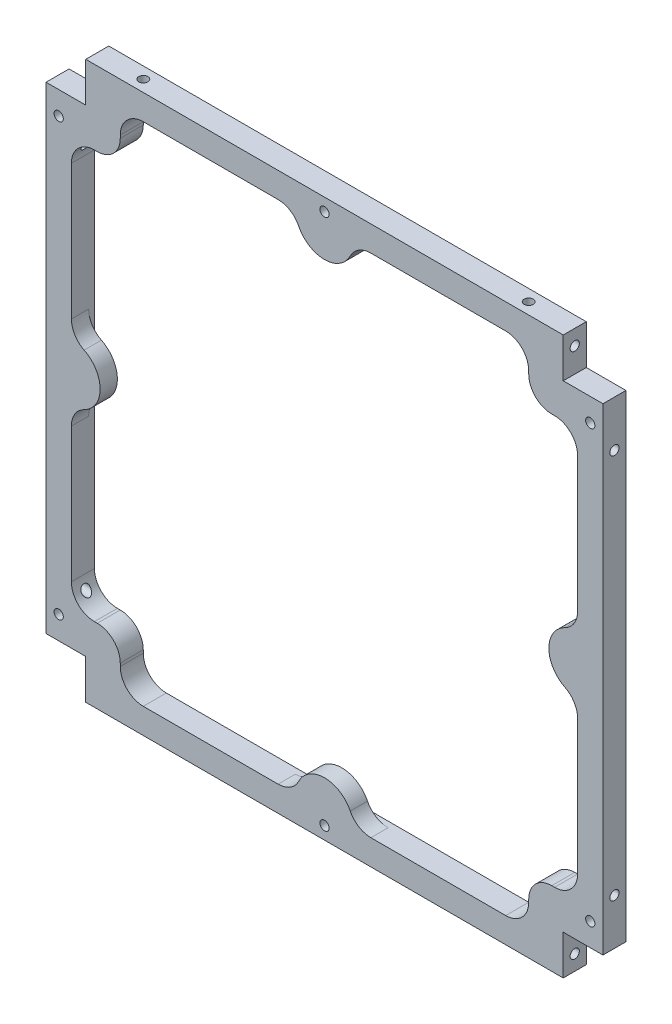
SolidWorks part; units mm, degrees
material "6061-T6 (SS)"
ref_plane "Front Plane" through (0, 0, 0) normal (0, 0, 1) x (1, 0, 0)
ref_plane "Top Plane" through (0, 0, 0) normal (0, 1, 0) x (1, 0, 0)
ref_plane "Right Plane" through (0, 0, 0) normal (1, 0, 0) x (0, 0, -1)
sketch "Sketch3" plane through (0, 0, 0) normal (0, 0, 1) x (1, 0, 0)
  line L1 (0, 0) -> (100, 0)
  line L2 (0, 0) -> (0, -100)
  line L3 (0, -100) -> (100, -100)
  line L4 (100, 0) -> (100, -100)
  dimension "D1" = 100
  dimension "D2" = 100
extrude "Boss-Extrude2" add sketch "Sketch3" along normal blind 4
sketch "Sketch4" plane through (0, 0, 0) normal (0, 0, -1) x (-1, 0, 0)
  line L1 (0, -100) -> (-8.5, -100)
  line L2 (0, -100) -> (0, -91.5)
  line L3 (0, -91.5) -> (-8.5, -91.5)
  line L4 (-8.5, -100) -> (-8.5, -91.5)
  line L5 (0, 0) -> (-8.5, 0)
  line L6 (0, 0) -> (0, -8.5)
  line L7 (0, -8.5) -> (-8.5, -8.5)
  line L8 (-8.5, 0) -> (-8.5, -8.5)
  line L9 (-100, 0) -> (-91.5, 0)
  line L10 (-100, 0) -> (-100, -8.5)
  line L11 (-100, -8.5) -> (-91.5, -8.5)
  line L12 (-91.5, 0) -> (-91.5, -8.5)
  line L14 (-100, -100) -> (-91.5, -100)
  line L15 (-100, -100) -> (-100, -91.5)
  line L16 (-100, -91.5) -> (-91.5, -91.5)
  line L17 (-91.5, -100) -> (-91.5, -91.5)
  dimension "D1" = 8.5
extrude "Cut-Extrude1" cut sketch "Sketch4" against normal through all
sketch "Sketch5" plane through (0, 0, 0) normal (0, 0, -1) x (-1, 0, 0)
  line L0 (-100, -91.5) -> (-100, -8.5) construction
  line L1 (-94, -14.5) -> (-85.5, -14.5)
  line L2 (-94, -14.5) -> (-94, -85.5)
  line L3 (-94, -85.5) -> (-85.5, -85.5)
  line L4 (-6, -14.5) -> (-6, -85.5)
  line L5 (-14.5, -14.5) -> (-14.5, -6)
  line L6 (-8.5, -100) -> (-91.5, -100) construction
  line L8 (-85.5, -6) -> (-14.5, -6)
  line L9 (-14.5, -85.5) -> (-14.5, -94)
  line L10 (-14.5, -94) -> (-85.5, -94)
  line L11 (-85.5, -94) -> (-85.5, -85.5)
  line L12 (-85.5, -14.5) -> (-85.5, -6)
  line L13 (-14.5, -14.5) -> (-6, -14.5)
  line L14 (-91.5, -8.5) -> (-91.5, 0) construction
  line L15 (-8.5, 0) -> (-8.5, -8.5) construction
  line L16 (-100, -8.5) -> (-91.5, -8.5) construction
  line L18 (-14.5, -85.5) -> (-6, -85.5)
  line L19 (-91.5, -91.5) -> (-100, -91.5) construction
  line L21 (-91.5, 0) -> (-8.5, 0) construction
  line L22 (0, -8.5) -> (0, -91.5) construction
  dimension "D1" = 6
  dimension "D2" = 6
  dimension "D3" = 6
  dimension "D4" = 6
  dimension "D5" = 6
  dimension "D6" = 6
  dimension "D7" = 6
  dimension "D8" = 6
extrude "Cut-Extrude2" cut sketch "Sketch5" against normal through all
fillet "Fillet4" radius 4 4 edges at (85.5, -85.5, 2) (14.5, -85.5, 2) (14.5, -14.5, 2) (85.5, -14.5, 2)
fillet "Fillet6" radius 4 8 edges at (85.5, -94, 2) (14.5, -94, 2) (6, -85.5, 2) (14.5, -6, 2) (6, -14.5, 2) (85.5, -6, 2) (94, -14.5, 2) (94, -85.5, 2)
sketch "Sketch6" plane through (0, 0, 4) normal (0, 0, 1) x (1, 0, 0)
  line L0 (6, -81.5) -> (6, -18.5) construction
  line L1 (94, -18.5) -> (94, -81.5) construction
  line L2 (6, -45) -> (6, -55)
  line L3 (94, -45) -> (94, -55)
  line L4 (18.5, -6) -> (81.5, -6) construction
  line L5 (81.5, -94) -> (18.5, -94) construction
  line L6 (45, -6) -> (55, -6)
  line L7 (45, -94) -> (55, -94)
  arc A0 (6, -55) -> (6, -45) centre (6, -50) ccw
  arc A1 (94, -45) -> (94, -55) centre (94, -50) ccw
  arc A2 (45, -6) -> (55, -6) centre (50, -6) ccw
  arc A3 (55, -94) -> (45, -94) centre (50, -94) ccw
  dimension "D1" = 10
  dimension "D2" = 10
  dimension "D3" = 10
  dimension "D4" = 10
extrude "Boss-Extrude3" add sketch "Sketch6" against normal offset from surface (3 mm away) 1 up to face at (50, -50, 0)
hole_wizard "M2x0.4 Tapped Hole1" positions "Sketch8" profile "Sketch7" tap size "M2x0.4" standard "ANSI Metric"
sketch "Sketch8" plane through (0, 0, 4) normal (0, 0, 1) x (1, 0, 0)
  line L1 (45, -94) -> (18.5, -94) construction
  line L2 (6, -45) -> (6, -18.5) construction
  line L3 (55, -6) -> (81.5, -6) construction
  line L4 (94, -55) -> (94, -81.5) construction
  line L5 (6, -81.5) -> (6, -55) construction
  line L6 (8.5, -8.5) -> (0, -8.5) construction
  line L7 (0, -91.5) -> (8.5, -91.5) construction
  line L8 (94, -18.5) -> (94, -45) construction
  line L9 (91.5, -91.5) -> (100, -91.5) construction
  line L10 (100, -8.5) -> (91.5, -8.5) construction
  point P12 (50, -3.8)
  point P14 (3.8, -12.5)
  point P16 (50, -96.2)
  point P18 (96.2, -87.5)
  point P29 (3.8, -87.5)
  point P38 (96.2, -12.5)
  dimension "D1" = 2.2
  dimension "D2" = 2.2
  dimension "D3" = 2.2
  dimension "D4" = 2.2
  dimension "D5" = 2.2
  dimension "D6" = 4
  dimension "D7" = 4
  dimension "D8" = 2.2
  dimension "D9" = 4
  dimension "D10" = 4
sketch "Sketch7" plane through (50, -3.8, 4) normal (1, 0, 0) x (0, -1, 0)
  line L0 (0, 0) -> (0, 5.6807)
  line L1 (0, 5.6807) -> (0.8, 5.2)
  line L2 (0.8, 5.2) -> (0.8, 0)
  line L5 (0.8, 0) -> (0, 0)
  line L10 (0, 5.6807) -> (-0.8, 5.2) construction
  line L11 (0, -6.35) -> (0, 107.95) construction
  dimension "Tap Drill Dia." = 1.6
  dimension "Tap Drill Depth" = 5.2
  dimension "Drill Angle" = 118
cosmetic thread "Hole Thread9" parameters "D1"=4, "D2"=2
cosmetic thread "Hole Thread10" parameters "D1"=4, "D2"=2
cosmetic thread "Hole Thread11" parameters "D1"=4, "D2"=2
cosmetic thread "Hole Thread12" parameters "D1"=4, "D2"=2
cosmetic thread "Cosmetic Thread1" parameters "D1"=4, "D2"=2
cosmetic thread "Cosmetic Thread2" parameters "D1"=4, "D2"=2
hole_wizard "M2x0.4 Tapped Hole2" positions "Sketch10" profile "Sketch9" tap size "M2x0.4" standard "ANSI Metric"
sketch "Sketch10" plane through (0, 0, 0) normal (0, 1, 0) x (1, 0, 0)
  line L0 (18.5, 0) -> (81.5, 0) construction
  line L1 (91.5, -4) -> (91.5, 0) construction
  line L2 (8.5, -4) -> (8.5, 0) construction
  point P10 (83.5, -2)
  point P13 (16.5, -2)
  dimension "D1" = 2
  dimension "D2" = 8
  dimension "D3" = 8
cosmetic thread "Hole Thread31" parameters "D2"=2
cosmetic thread "Hole Thread32" parameters "D2"=2
sketch "Sketch9" plane through (83.5, 0, 2) normal (1, 0, 0) x (0, 0, 1)
  line L0 (0, 0) -> (0, 6.5359)
  line L1 (0, 6.5359) -> (0.8, 6.5359)
  line L2 (0.8, 6.5359) -> (0.8, 0)
  line L5 (0.8, 0) -> (0, 0)
  line L11 (0, -6.35) -> (0, 107.95) construction
  dimension "Thru Tap Drill Dia." = 1.6
  dimension "Thru Tap Drill Depth" = 6.5359
hole_wizard "M2x0.4 Tapped Hole3" positions "Sketch12" profile "Sketch11" tap size "M2x0.4" standard "ANSI Metric"
sketch "Sketch12" plane through (100, 0, 0) normal (1, 0, 0) x (0, 0, -1)
  line L0 (0, -91.5) -> (0, -8.5) construction
  line L1 (-4, -8.5) -> (0, -8.5) construction
  line L2 (-4, -91.5) -> (0, -91.5) construction
  point P0 (-2, -83.5)
  point P3 (-2, -16.5)
  dimension "D1" = 2
  dimension "D2" = 8
  dimension "D3" = 8
cosmetic thread "Hole Thread30" parameters "D1"=4, "D2"=2
cosmetic thread "Hole Thread33" parameters "D1"=4, "D2"=2
sketch "Sketch11" plane through (100, -83.5, 2) normal (0, 1, 0) x (0, 0, -1)
  line L0 (0, 0) -> (0, 9.0007)
  line L1 (0, 9.0007) -> (0.8, 8.52)
  line L2 (0.8, 8.52) -> (0.8, 0)
  line L5 (0.8, 0) -> (0, 0)
  line L10 (0, 9.0007) -> (-0.8, 8.52) construction
  line L11 (0, -6.35) -> (0, 107.95) construction
  dimension "Tap Drill Dia." = 1.6
  dimension "Tap Drill Depth" = 8.52
  dimension "Drill Angle" = 118
hole_wizard "M2x0.4 Tapped Hole13" positions "Sketch16" profile "Sketch15" tap size "M2x0.4" standard "Ansi Metric" end condition up to next
sketch "Sketch16" plane through (0, 0, 0) normal (-1, 0, 0) x (0, 0, 1)
  line L0 (4, -8.5) -> (4, -91.5) construction
  line L1 (4, -91.5) -> (0, -91.5) construction
  line L2 (4, -8.5) -> (0, -8.5) construction
  point P3 (2, -83.5)
  point P18 (2, -16.5)
  dimension "D1" = 2
  dimension "D2" = 8
  dimension "D3" = 8
cosmetic thread "Hole Thread22" parameters "D2"=2
cosmetic thread "Hole Thread34" parameters "D2"=2
sketch "Sketch15" plane through (0, -83.5, 2) normal (0, 1, 0) x (0, 0, 1)
  line L0 (0, 0) -> (0, 6.5359)
  line L1 (0, 6.5359) -> (0.8, 6.5359)
  line L2 (0.8, 6.5359) -> (0.8, 0)
  line L5 (0.8, 0) -> (0, 0)
  line L11 (0, -6.35) -> (0, 107.95) construction
  dimension "次ｻｰﾌｪｽまでのねじ下穴ﾄﾞﾘﾙ直径" = 1.6
  dimension "次ｻｰﾌｪｽまでのねじ下穴ﾄﾞﾘﾙの深さ" = 6.5359
hole_wizard "M2x0.4 Tapped Hole5" positions "Sketch18" profile "Sketch17" tap size "M2x0.4" standard "ANSI Metric"
sketch "Sketch18" plane through (0, -100, 0) normal (0, -1, 0) x (-1, 0, 0)
  line L0 (-8.5, -4) -> (-91.5, -4) construction
  line L1 (-8.5, -4) -> (-8.5, 0) construction
  line L2 (-91.5, -4) -> (-91.5, 0) construction
  point P0 (-16.5, -2)
  point P3 (-83.5, -2)
  dimension "D1" = 2
  dimension "D2" = 8
  dimension "D3" = 8
sketch "Sketch17" plane through (16.5, -100, 2) normal (1, 0, 0) x (0, 0, -1)
  line L0 (0, 0) -> (0, 6.4807)
  line L1 (0, 6.4807) -> (0.8, 6)
  line L2 (0.8, 6) -> (0.8, 0)
  line L5 (0.8, 0) -> (0, 0)
  line L10 (0, 6.4807) -> (-0.8, 6) construction
  line L11 (0, -6.35) -> (0, 107.95) construction
  dimension "Tap Drill Dia." = 1.6
  dimension "Tap Drill Depth" = 6
  dimension "Drill Angle" = 118
cosmetic thread "Hole Thread23" parameters "D1"=4, "D2"=2
cosmetic thread "Hole Thread24" parameters "D1"=4, "D2"=2
fillet "Fillet7" radius 4 1 edges at (6, -45, 2.5)
fillet "Fillet8" radius 4 7 edges at (45, -94, 2.5) (55, -94, 2.5) (45, -6, 2.5) (55, -6, 2.5) (94, -45, 2.5) (94, -55, 2.5) (6, -55, 2.5)
hole_wizard "M2x0.4 Tapped Hole9" positions "Sketch30" profile "Sketch29" tap size "M2x0.4" standard "ANSI Metric"
sketch "Sketch30" plane through (8.5, 0, 0) normal (-1, 0, 0) x (0, 0, 1)
  point P0 (2, -95.75)
sketch "Sketch29" plane through (8.5, -95.75, 2) normal (0, 1, 0) x (0, 0, 1)
  line L0 (0, 0) -> (0, 6.4807)
  line L1 (0, 6.4807) -> (0.8, 6)
  line L2 (0.8, 6) -> (0.8, 0)
  line L5 (0.8, 0) -> (0, 0)
  line L10 (0, 6.4807) -> (-0.8, 6) construction
  line L11 (0, -6.35) -> (0, 107.95) construction
  dimension "Tap Drill Dia." = 1.6
  dimension "Tap Drill Depth" = 6
  dimension "Drill Angle" = 118
cosmetic thread "Hole Thread35" parameters "D1"=4, "D2"=2
hole_wizard "M2x0.4 Tapped Hole10" positions "Sketch32" profile "Sketch31" tap size "M2x0.4" standard "ANSI Metric"
sketch "Sketch32" plane through (8.5, 0, 0) normal (-1, 0, 0) x (0, 0, 1)
  point P0 (2, -4.25)
sketch "Sketch31" plane through (8.5, -4.25, 2) normal (0, 1, 0) x (0, 0, 1)
  line L0 (0, 0) -> (0, 6.4807)
  line L1 (0, 6.4807) -> (0.8, 6)
  line L2 (0.8, 6) -> (0.8, 0)
  line L5 (0.8, 0) -> (0, 0)
  line L10 (0, 6.4807) -> (-0.8, 6) construction
  line L11 (0, -6.35) -> (0, 107.95) construction
  dimension "Tap Drill Dia." = 1.6
  dimension "Tap Drill Depth" = 6
  dimension "Drill Angle" = 118
cosmetic thread "Hole Thread36" parameters "D1"=4, "D2"=2
sketch "Sketch33" plane through (0, 0, 4) normal (0, 0, 1) x (1, 0, 0)
  line L0 (91.5, -100) -> (91.5, -91.5) construction
  line L1 (8.5, -100) -> (91.5, -100)
  line L2 (8.5, -100) -> (8.5, -98.4)
  line L3 (8.5, -98.4) -> (91.5, -98.4)
  line L4 (91.5, -100) -> (91.5, -98.4)
  line L5 (100, -8.5) -> (91.5, -8.5) construction
  line L6 (100, -91.5) -> (98.4, -91.5)
  line L7 (100, -91.5) -> (100, -8.5)
  line L8 (100, -8.5) -> (98.4, -8.5)
  line L9 (98.4, -91.5) -> (98.4, -8.5)
  line L10 (8.5, 0) -> (8.5, -8.5) construction
  line L11 (91.5, 0) -> (8.5, 0)
  line L12 (91.5, 0) -> (91.5, -1.6)
  line L13 (91.5, -1.6) -> (8.5, -1.6)
  line L14 (8.5, 0) -> (8.5, -1.6)
  line L15 (0, -91.5) -> (8.5, -91.5) construction
  line L16 (0, -8.5) -> (1.6, -8.5)
  line L17 (0, -8.5) -> (0, -91.5)
  line L18 (0, -91.5) -> (1.6, -91.5)
  line L19 (1.6, -8.5) -> (1.6, -91.5)
  dimension "D1" = 1.6
  dimension "D2" = 1.6
  dimension "D3" = 1.6
  dimension "D4" = 1.6
extrude "Cut-Extrude3" cut sketch "Sketch33" against normal blind 10
sketch "Sketch35" plane through (91.5, 0, 0) normal (1, 0, 0) x (0, 0, -1)
  line L2 (0, -98.4) -> (0, -91.5) construction
  line L3 (0, -98.4) -> (-4, -98.4) construction
  point P1 (-2, -95.75)
  dimension "D1" = 2
  dimension "D2" = 2.65
hole_wizard "M2x0.4 Tapped Hole11" positions "Sketch37" profile "Sketch36" tap size "M2x0.4" standard "ANSI Metric"
sketch "Sketch37" plane through (91.5, 0, 0) normal (1, 0, 0) x (0, 0, -1)
  point P0 (-2, -95.75)
sketch "Sketch36" plane through (91.5, -95.75, 2) normal (0, 1, 0) x (0, 0, -1)
  line L0 (0, 0) -> (0, 6.4807)
  line L1 (0, 6.4807) -> (0.8, 6)
  line L2 (0.8, 6) -> (0.8, 0)
  line L5 (0.8, 0) -> (0, 0)
  line L10 (0, 6.4807) -> (-0.8, 6) construction
  line L11 (0, -6.35) -> (0, 107.95) construction
  dimension "Tap Drill Dia." = 1.6
  dimension "Tap Drill Depth" = 6
  dimension "Drill Angle" = 118
cosmetic thread "Hole Thread37" parameters "D1"=4, "D2"=2
sketch "Sketch38" plane through (91.5, 0, 0) normal (1, 0, 0) x (0, 0, -1)
  line L0 (0, -1.6) -> (-4, -1.6) construction
  line L1 (0, -8.5) -> (0, -1.6) construction
  point P0 (-2, -4.25)
  dimension "D1" = 2.65
  dimension "D2" = 2
hole_wizard "M2x0.4 Tapped Hole12" positions "Sketch40" profile "Sketch39" tap size "M2x0.4" standard "ANSI Metric"
sketch "Sketch40" plane through (91.5, 0, 0) normal (1, 0, 0) x (0, 0, -1)
  point P0 (-2, -4.25)
sketch "Sketch39" plane through (91.5, -4.25, 2) normal (0, 1, 0) x (0, 0, -1)
  line L0 (0, 0) -> (0, 6.4807)
  line L1 (0, 6.4807) -> (0.8, 6)
  line L2 (0.8, 6) -> (0.8, 0)
  line L5 (0.8, 0) -> (0, 0)
  line L10 (0, 6.4807) -> (-0.8, 6) construction
  line L11 (0, -6.35) -> (0, 107.95) construction
  dimension "Tap Drill Dia." = 1.6
  dimension "Tap Drill Depth" = 6
  dimension "Drill Angle" = 118
cosmetic thread "Hole Thread38" parameters "D1"=4, "D2"=2
